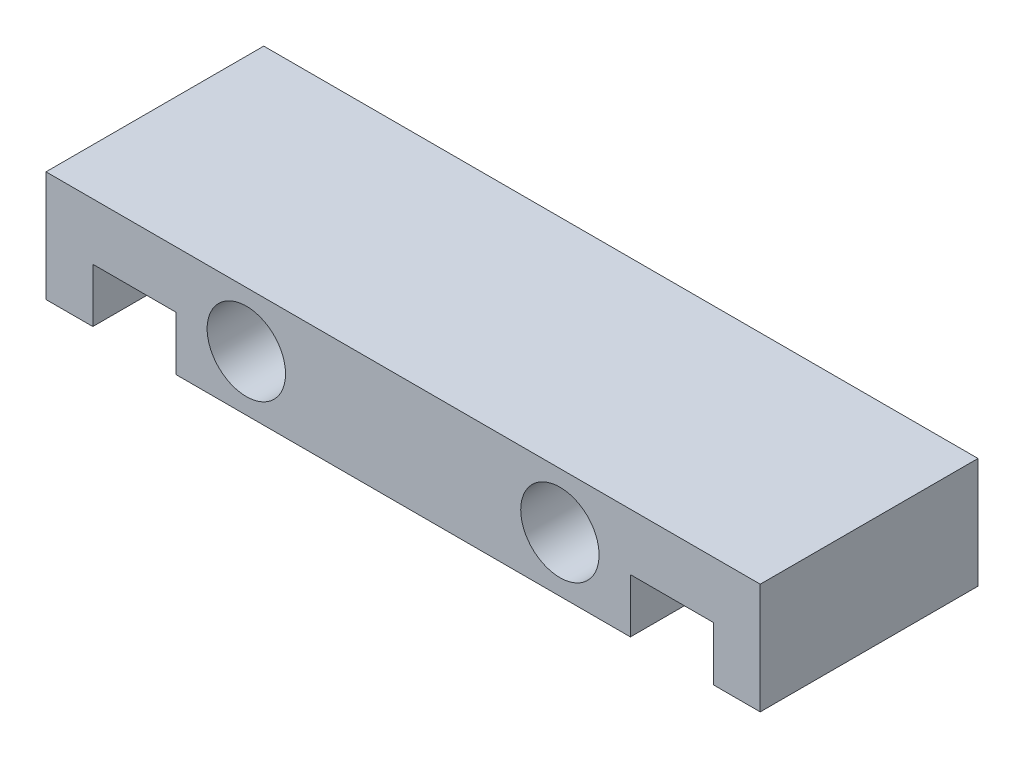
SolidWorks part; units mm, degrees
material "Tuffak AP"
ref_plane "Front Plane" through (0, 0, 0) normal (0, 0, 1) x (1, 0, 0)
ref_plane "Top Plane" through (0, 0, 0) normal (0, 1, 0) x (1, 0, 0)
ref_plane "Right Plane" through (0, 0, 0) normal (1, 0, 0) x (0, 0, -1)
sketch "Sketch1" plane through (0, 0, 0) normal (0, 1, 0) x (1, 0, 0)
  line L1 (0, 0) -> (82, 0)
  line L2 (0, 0) -> (0, 25)
  line L3 (0, 25) -> (82, 25)
  line L4 (82, 0) -> (82, 25)
  dimension "D1" = 82
  dimension "D2" = 25
extrude "Boss-Extrude1" add sketch "Sketch1" along normal blind 12.7
sketch "Sketch2" plane through (0, 0, 0) normal (0, 0, 1) x (1, 0, 0)
  line L0 (0, 0) -> (82, 0) construction
  line L1 (5.375, 6.2) -> (14.905, 6.2)
  line L2 (5.375, 6.2) -> (5.375, 0)
  line L3 (5.375, 0) -> (14.905, 0)
  line L4 (14.905, 6.2) -> (14.905, 0)
  line L5 (0, 12.7) -> (0, 0) construction
  dimension "D1" = 5.375
  dimension "D2" = 9.53
  dimension "D3" = 6.2
extrude "Cut-Extrude1" cut sketch "Sketch2" against normal through all
ref_plane "Plane1" through (41, 0, 0) normal (1, 0, 0) x (0, 0, -1)
sketch "Sketch3" plane through (0, 0, 0) normal (0, 0, 1) x (1, 0, 0)
  line L0 (0, 12.7) -> (82, 12.7) construction
  line L2 (0, 12.7) -> (0, 0) construction
  circle A0 centre (23, 6.35) radius 4.5
  dimension "D3" = 9
  dimension "D1" = 6.35
  dimension "D2" = 23
extrude "Cut-Extrude2" cut sketch "Sketch3" against normal blind 13
mirror "Mirror1" about plane through (41, 0, 0) normal (1, 0, 0) of "Cut-Extrude2", "Cut-Extrude1"
